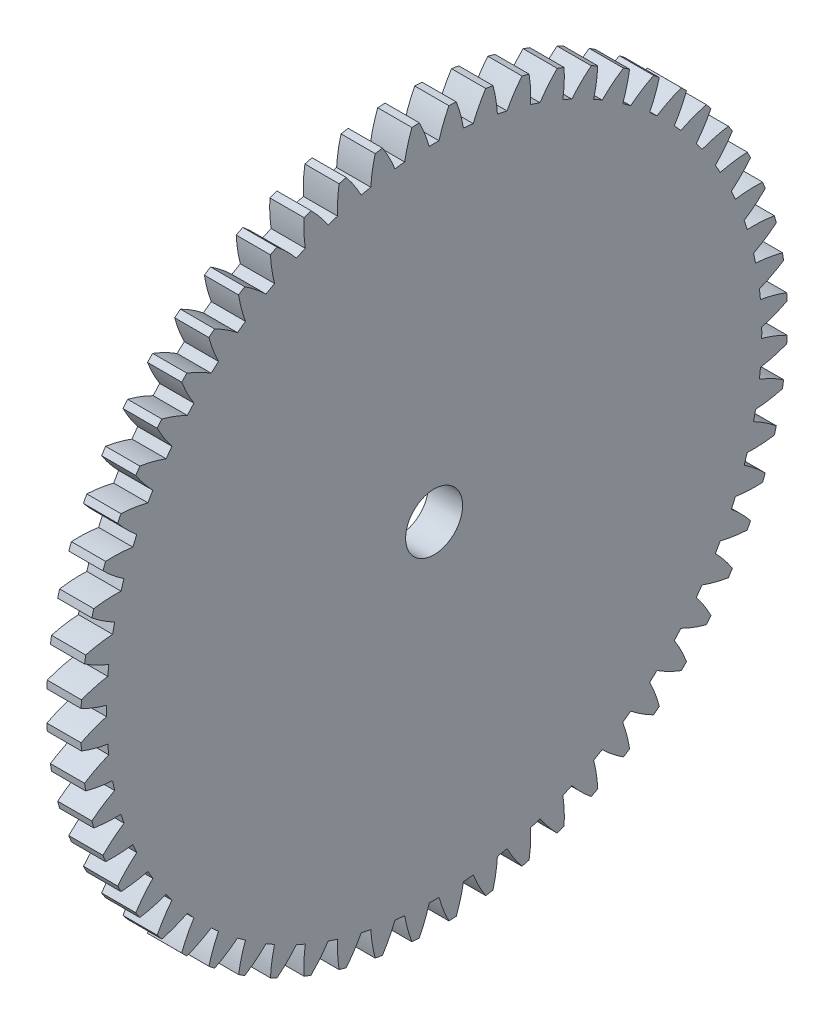
SolidWorks part; units mm, degrees
ref_plane "Plane1" through (0, 0, 0) normal (0, 0, 1) x (1, 0, 0)
ref_plane "Plane2" through (0, 0, 0) normal (0, 1, 0) x (1, 0, 0)
ref_plane "Plane3" through (0, 0, 0) normal (1, 0, 0) x (0, 0, -1)
sketch "HoldingSke" plane through (0, 0, 0) normal (0, 1, 0) x (1, 0, 0)
  line L0 (0, 0) -> (0.5, -0.866)
  line L1 (-15, 0) -> (100, 0) construction
  line L2 (0, 0) -> (-2.1039, 2.3779)
  line L3 (0, 0) -> (-11.863, 4.5341)
  line L4 (0, 0) -> (4.318, 7.479)
  line L5 (0, 0) -> (-46.8476, -17.4728)
  line L6 (0, 0) -> (-2.4869, -1.6779)
  line L7 (-2.1039, 2.3779) -> (8.6586, 51.2059)
  line L8 (-76.2, 54.61) -> (-75.3, 54.61)
  line L9 (-71.009, 38.7566) -> (-53.1078, 45.2721)
  line L10 (-76.2, 71.12) -> (104.1128, 71.12)
  line L11 (0, 0) -> (-3, 0)
  line L12 (-76.2, 101.6) -> (-76.162, 101.6)
  line L13 (24.9733, 27.94) -> (52.9518, 28.4284)
  line L14 (24.9733, 27.94) -> (24.9743, 27.94)
  line L15 (24.9733, 27.94) -> (100.4006, 29.5858)
  line L16 (-63.627, -1) -> (-12.827, -1)
  circle A0 centre (0, 0) radius 2.5
  circle A1 centre (0, 0) radius 28.749
  circle A2 centre (0, 0) radius 37.5
  circle A3 centre (0, 0) radius 2.5
  dimension "MHD" = 57.498
  dimension "Hub_dia" = 75
  dimension "Bore" = 5
  dimension "MBD" = 5
  dimension "Num_teeth" = 60
  dimension "Pitch_radius" = 180.3128
  dimension "Pitch" = 1
  dimension "Width" = 3
  dimension "Overall_len" = 50
  dimension "Show_teeth" = 60
  dimension "Thickness" = 3
  dimension "OAL" = 50.0001
  dimension "T_dim" = 0.9
  dimension "Ap" = 20
  dimension "H" = 19.05
  dimension "Backlash" = 0.038
  dimension "Addendum_fac" = 1
  dimension "Dedendum_fac" = 1.25
  dimension "Clearance_fac" = 0.25
  dimension "Dedendum_add" = 0.001
  dimension "Module" = 1
sketch "BasProSke" plane through (0, 0, 0) normal (0, 1, 0) x (1, 0, 0)
  line L0 (-10, 0) -> (60, 0) construction
  line L1 (0, 0) -> (0, 31)
  line L2 (0, 0) -> (3, 0)
  line L3 (3, 0) -> (3, 31)
  line L4 (3, 31) -> (0, 31)
  dimension "Diameter" = 62
  dimension "Thickness" = 3
revolve "Base-Revolve" add sketch "BasProSke" angle 360 about L0
sketch "TooCutSke" plane through (0, 0, 0) normal (1, 0, 0) x (0, 0, -1)
  line L1 (0, 0) -> (0, 107) construction
  line L2 (0, 0) -> (-0.8518, 29.9879) construction
  line L3 (0, 0) -> (-3.1393, 59.9006) construction
  line L4 (-0.8518, 29.9879) -> (-1.5696, 29.9503) construction
  arc A0 (0.4302, 28.7458) -> (-0.4302, 28.7458) centre (0, 0) ccw
  arc A1 (1.3127, 30.9976) -> (-1.3127, 30.9976) centre (0, 0) ccw
  circle A2 centre (0, 0) radius 30 construction
  circle A3 centre (0, 0) radius 28.1908 construction
  arc A4 (-0.4302, 28.7458) -> (-1.3127, 30.9976) centre (-11.9871, 25.5153) ccw
  arc A5 (1.3127, 30.9976) -> (0.4302, 28.7458) centre (11.9871, 25.5153) ccw
  dimension "Root_dia" = 57.498
  dimension "Overcut_dia" = 62.0508
  dimension "Pitch_dia" = 60
  dimension "Base_dia" = 56.3816
  dimension "Flank_rad" = 12
  dimension "Half_ang" = 3
  dimension "Half_CT" = 0.7188
extrude "ToothCut" cut sketch "TooCutSke" along normal through all
fillet "Breaks" [suppressed] radius 0.02
fillet "RootFillets" [suppressed] radius 0.251
pattern_circular "TeethCuts" count 60 every 6 about axis through (-10, 0, 0) along (1, 0, 0) of "ToothCut", "RootFillets", "Breaks"
sketch "HubNeaOneSke" plane through (0, 0, 0) normal (-1, 0, 0) x (0, 0, 1)
  circle A0 centre (0, 0) radius 28.749
  dimension "Diameter" = 57.498
extrude "HubNearOne" [suppressed] add sketch "HubNeaOneSke" along normal blind 47.0001
sketch "HubNeaBotSke" plane through (0, 0, 0) normal (-1, 0, 0) x (0, 0, 1)
  circle A0 centre (0, 0) radius 28.749
  dimension "Diameter" = 57.498
extrude "HubNearBoth" [suppressed] add sketch "HubNeaBotSke" along normal blind 23.5
ref_plane "FarPln" through (3, 0, 0) normal (1, 0, 0) x (0, 0, -1)
sketch "HubFarSke" plane through (3, 0, 0) normal (1, 0, 0) x (0, 0, -1)
  circle A0 centre (0, 0) radius 28.749
  dimension "Diameter" = 57.498
extrude "HubFar" [suppressed] add sketch "HubFarSke" along normal blind 23.5
sketch "BorSke" plane through (0, 0, 0) normal (1, 0, 0) x (0, 0, -1)
  circle A0 centre (0, 0) radius 2.5
  dimension "Diameter" = 5
extrude "Bore" cut sketch "BorSke" along normal mid plane 100.0001
sketch "KeySke" plane through (0, 0, 0) normal (1, 0, 0) x (0, 0, -1)
  line L0 (-1, 0) -> (-1, 3.4)
  line L1 (-1, 3.4) -> (1, 3.4)
  line L2 (1, 3.4) -> (1, 0)
  line L3 (0, 0) -> (0, 34) construction
  line L4 (-1, 0) -> (1, 0)
  dimension "Offset" = 3.4
  dimension "Width" = 2
extrude "Keyway" [suppressed] cut sketch "KeySke" along normal mid plane 100.0001
pattern_circular "Keyway2" [suppressed] count 2 every 90 about axis through (-10, 0, 0) along (1, 0, 0)
equation "' \"Module@HoldingSke\" = 6.35"
equation "' \"Num_teeth@HoldingSke\" = 12"
equation "' \"Ap@HoldingSke\" =  20"
equation "' \"Width@HoldingSke\" = 0.5 * 25.4"
equation "' \"Hub_dia@HoldingSke\"= 1 * 25.4"
equation "' \"Overall_len@HoldingSke\" = 1.0 * 25.4"
equation "' \"Bore@HoldingSke\" = 0.75 * 25.4"
equation "' \"T_dim@HoldingSke\" = 0.1 * 25.4"
equation "' \"Width@KeySke\" = 0.25 * 25.4"
equation "' \"Show_teeth@HoldingSke\" = 13"
equation "' \"Backlash@HoldingSke\" = 0.009 * 25.4"
equation "' \"Addendum_fac@HoldingSke\" = 1.0"
equation "' \"Dedendum_fac@HoldingSke\" = 1.25"
equation "' \"Dedendum_add@HoldingSke\" = 0.00005 * 25.4"
equation "' \"Clearance_fac@HoldingSke\" = 0.25"
equation "\"Pitch@HoldingSke\" = 1 / \"Module@HoldingSke\""
equation "\"Overcut_dia@TooCutSke\" = (\"Num_teeth@HoldingSke\" + 2 * \"Addendum_fac@HoldingSke\") / \"Pitch@HoldingSke\" + 0.002 * 25.4"
equation "\"Pitch_dia@TooCutSke\" = \"Num_teeth@HoldingSke\" / \"Pitch@HoldingSke\""
equation "\"Base_dia@TooCutSke\" = \"Num_teeth@HoldingSke\" / \"Pitch@HoldingSke\" * cos((\"Ap@HoldingSke\"  * 3.14159265 / 180))"
equation "\"Root_dia@TooCutSke\" = (\"Num_teeth@HoldingSke\" + 2) / \"Pitch@HoldingSke\" - 2 * (\"Addendum_fac@HoldingSke\" + \"Dedendum_fac@HoldingSke\") / \"Pitch@HoldingSke\" - \"Dedendum_add@HoldingSke\" * 2"
equation "\"Half_ang@TooCutSke\" = 180 / \"Num_teeth@HoldingSke\""
equation "\"Half_CT@TooCutSke\" = \"Num_teeth@HoldingSke\" / \"Pitch@HoldingSke\" * sin((3.14159265 / 2 / \"Num_teeth@HoldingSke\")) / 2 - 7 * \"Backlash@HoldingSke\" / 4"
equation "\"Flank_rad@TooCutSke\" = \"Num_teeth@HoldingSke\" / \"Pitch@HoldingSke\" / 5"
equation "\"Radius@RootFillets\" = \"Clearance_fac@HoldingSke\" / \"Pitch@HoldingSke\" + \"Dedendum_add@HoldingSke\""
equation "\"Break_rad@Breaks\" = 0.02 / \"Pitch@HoldingSke\""
equation "\"Thickness@HoldingSke\" = \"Width@HoldingSke\""
equation "\"OAL@HoldingSke\" = \"Thickness@HoldingSke\""
equation "\"MHD@HoldingSke\" = (\"Num_teeth@HoldingSke\" + 2) / \"Pitch@HoldingSke\" - 2 * (\"Addendum_fac@HoldingSke\" + \"Dedendum_fac@HoldingSke\")  / \"Pitch@HoldingSke\" - \"Dedendum_add@HoldingSke\" * 2"
equation "\"MBD@HoldingSke\" = (\"Num_teeth@HoldingSke\" + 2) / \"Pitch@HoldingSke\" - 2 * (\"Addendum_fac@HoldingSke\" + \"Dedendum_fac@HoldingSke\")  / \"Pitch@HoldingSke\" - \"Dedendum_add@HoldingSke\" * 2 - 0.002 * 25.4"
equation "\"MHD@HoldingSke\" = ((sgn( \"MHD@HoldingSke\" - \"Hub_dia@HoldingSke\" )-1)*( \"MHD@HoldingSke\" - \"Hub_dia@HoldingSke\" ))/-2+ \"Hub_dia@HoldingSke\""
equation "\"MBD@HoldingSke\" = ((sgn( \"MBD@HoldingSke\" - \"Bore@HoldingSke\" )-1)*( \"MBD@HoldingSke\" - \"Bore@HoldingSke\" ))/-2+ \"Bore@HoldingSke\""
equation "\"OAL@HoldingSke\" = ((sgn( \"OAL@HoldingSke\" - \"Overall_len@HoldingSke\" )+1)*( \"OAL@HoldingSke\" - \"Overall_len@HoldingSke\" ))/2 + \"Overall_len@HoldingSke\" + 0.000002 * 25.4"
equation "\"Num_teeth@TeethCuts\" = int( \"Show_teeth@HoldingSke\" ) + 1"
equation "\"Num_teeth@TeethCuts\" = ((sgn( \"Num_teeth@TeethCuts\" - \"Num_teeth@HoldingSke\" )-1)*( \"Num_teeth@TeethCuts\" - \"Num_teeth@HoldingSke\" ))/-2+ \"Num_teeth@HoldingSke\""
equation "\"Num_teeth@TeethCuts\" = ((sgn( \"Num_teeth@TeethCuts\" - 2.0)+1)*( \"Num_teeth@TeethCuts\" - 2.0))/2 +2.0"
equation "\"Angle@TeethCuts\" = 360.0 / \"Num_teeth@HoldingSke\""
equation "\"Diameter@BasProSke\" = (\"Num_teeth@HoldingSke\" + 2 * \"Addendum_fac@HoldingSke\") / \"Pitch@HoldingSke\""
equation "\"Thickness@BasProSke\"  = \"Thickness@HoldingSke\""
equation "' \"Fillet_rad@BasProSke\" =  \"Thickness@HoldingSke\" * 0.05"
equation "\"MHD@HoldingSke\" = ((sgn( \"MHD@HoldingSke\" - \"Root_dia@TooCutSke\" )-1)*( \"MHD@HoldingSke\" - \"Root_dia@TooCutSke\" ))/-2+ \"Root_dia@TooCutSke\""
equation "\"Diameter@HubNeaOneSke\" = \"MHD@HoldingSke\""
equation "\"Length@HubNearOne\" = \"OAL@HoldingSke\" - \"Thickness@BasProSke\""
equation "\"Diameter@HubNeaBotSke\" = \"MHD@HoldingSke\""
equation "\"Length@HubNearBoth\" = ( \"OAL@HoldingSke\" - \"Thickness@BasProSke\" ) / 2.0"
equation "\"Thickness@FarPln\" = \"Thickness@BasProSke\""
equation "\"Diameter@HubFarSke\" = \"MHD@HoldingSke\""
equation "\"Length@HubFar\" = ( \"OAL@HoldingSke\" - \"Thickness@BasProSke\" ) / 2.0"
equation "\"Diameter@BorSke\" = \"MBD@HoldingSke\""
equation "\"D1@Bore\" = \"OAL@HoldingSke\" * 2.0"
equation "\"D1@Keyway\" = \"OAL@HoldingSke\" * 2.0"
equation "\"Offset@KeySke\" = \"T_dim@HoldingSke\" + \"MBD@HoldingSke\" / 2.0"
